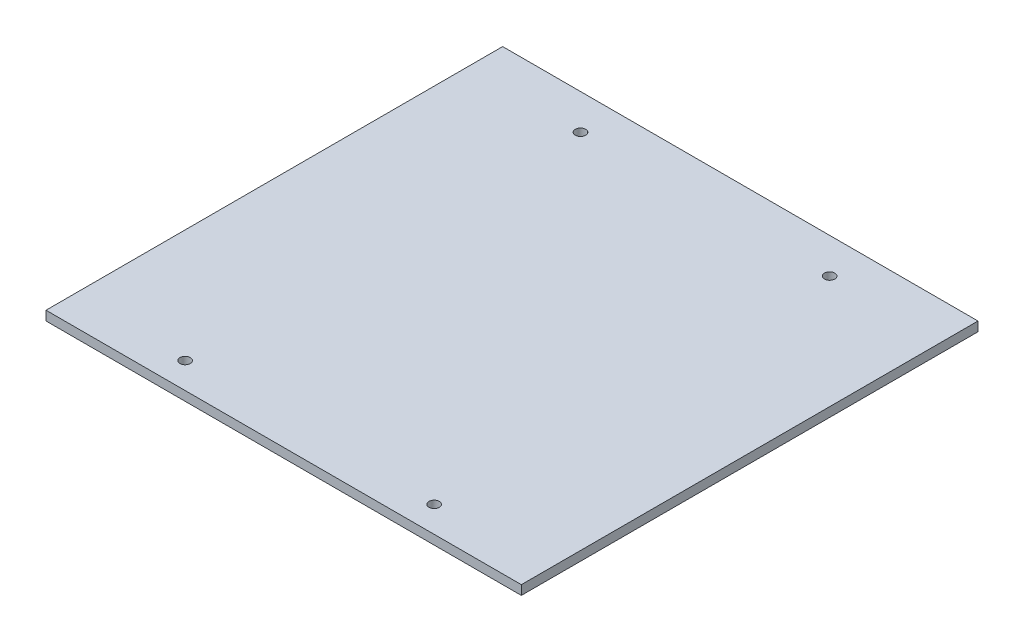
SolidWorks part; units mm, degrees
ref_plane "Front" through (0, 0, 0) normal (0, 0, 1) x (1, 0, 0)
ref_plane "Top" through (0, 0, 0) normal (0, 1, 0) x (1, 0, 0)
ref_plane "Right" through (0, 0, 0) normal (1, 0, 0) x (0, 0, -1)
sketch "Sketch1" plane through (0, 0, 0) normal (0, 1, 0) x (1, 0, 0)
  line L1 (-114.5, -110) -> (114.5, -110)
  line L2 (-114.5, -110) -> (-114.5, 110)
  line L3 (-114.5, 110) -> (114.5, 110)
  line L4 (114.5, -110) -> (114.5, 110)
  line L5 (-114.5, -110) -> (114.5, 110) construction
  line L6 (-114.5, 110) -> (114.5, -110) construction
  point P0 (0, 0)
  dimension "D1" = 229
  dimension "D2" = 220
extrude "Boss-Extrude1" add sketch "Sketch1" along normal blind 4.5
sketch "Sketch2" plane through (0, 0, 0) normal (0, -1, 0) x (1, 0, 0)
  circle A0 centre (-60, 97.5) radius 2.5
  circle A1 centre (60, 97.5) radius 2.5
  circle A2 centre (60, -93) radius 2.5
  circle A3 centre (-60, -93) radius 2.5
extrude "Cut-Extrude1" cut sketch "Sketch2" against normal up to next
